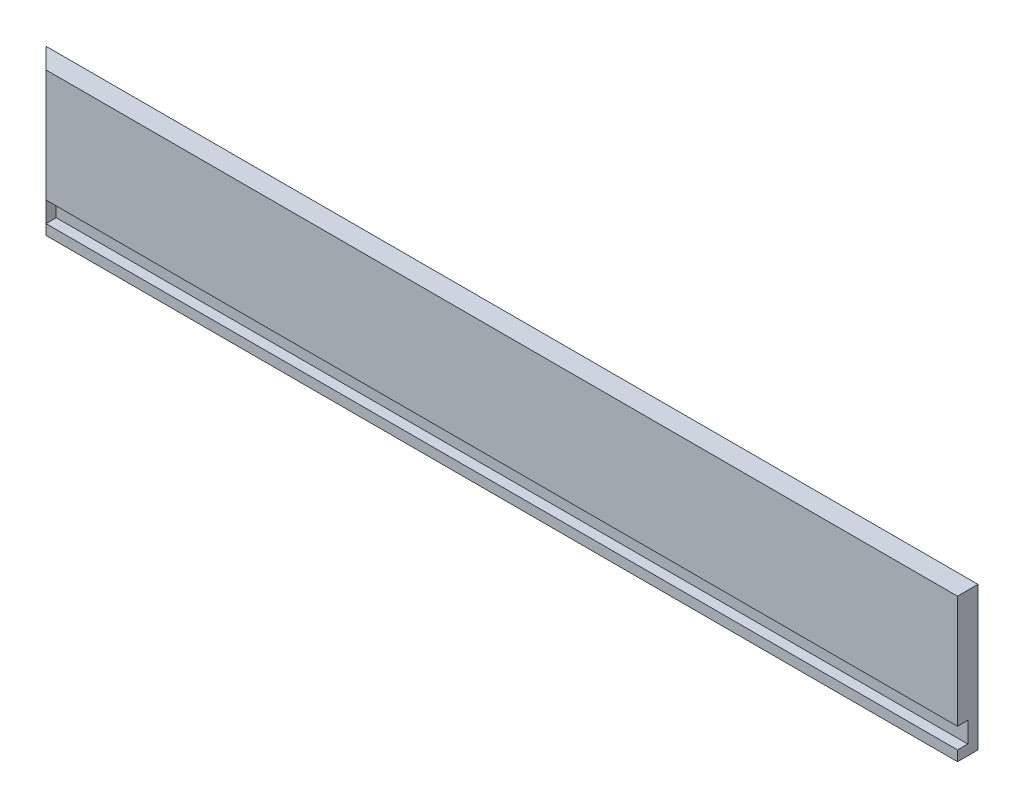
SolidWorks part; units mm, degrees
material "Cedar"
ref_plane "Front Plane" through (0, 0, 0) normal (0, 0, 1) x (1, 0, 0)
ref_plane "Top Plane" through (0, 0, 0) normal (0, 1, 0) x (1, 0, 0)
ref_plane "Right Plane" through (0, 0, 0) normal (1, 0, 0) x (0, 0, -1)
sketch "Sketch1" plane through (0, 0, 0) normal (0, 0, 1) x (1, 0, 0)
  line L1 (-213.644, 119.1326) -> (364.206, 119.1326)
  line L2 (-213.644, 119.1326) -> (-213.644, 30.2326)
  line L3 (-213.644, 30.2326) -> (364.206, 30.2326)
  line L4 (364.206, 119.1326) -> (364.206, 30.2326)
  dimension "D1" = 577.85
  dimension "D2" = 88.9
extrude "Boss-Extrude1" add sketch "Sketch1" along normal blind 12.7
sketch "Sketch2" plane through (0, 119.1326, 0) normal (0, 1, 0) x (1, 0, 0)
  line L0 (-200.944, -12.7) -> (-213.644, 0)
  line L1 (364.206, -12.7) -> (-213.644, -12.7) construction
  line L2 (-213.644, 0) -> (-213.644, -12.7)
  line L3 (-213.644, -12.7) -> (-200.944, -12.7)
  dimension "D1" = 45
extrude "Cut-Extrude1" cut sketch "Sketch2" against normal through all
sketch "Sketch4" plane through (0, 0, 12.7) normal (0, 0, 1) x (1, 0, 0)
  line L0 (-200.944, 30.2326) -> (-200.944, 119.1326) construction
  line L1 (-200.944, 49.2826) -> (364.206, 49.2826)
  line L2 (-200.944, 49.2826) -> (-200.944, 36.5826)
  line L3 (-200.944, 36.5826) -> (364.206, 36.5826)
  line L4 (364.206, 49.2826) -> (364.206, 36.5826)
  line L5 (364.206, 30.2326) -> (364.206, 119.1326) construction
  line L6 (-200.944, 30.2326) -> (364.206, 30.2326) construction
  dimension "D1" = 6.35
  dimension "D2" = 12.7
extrude "Cut-Extrude3" cut sketch "Sketch4" against normal blind 6.35
